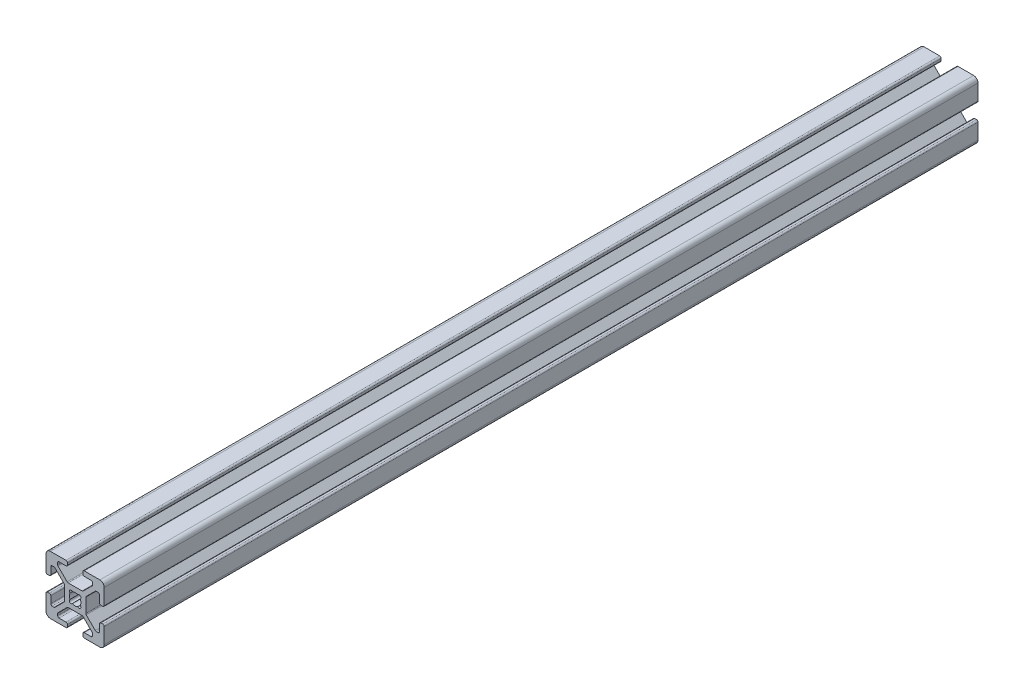
SolidWorks part; units mm, degrees
ref_plane "Front Plane" through (0, 0, 0) normal (0, 0, 1) x (1, 0, 0)
ref_plane "Top Plane" through (0, 0, 0) normal (0, 1, 0) x (1, 0, 0)
ref_plane "Right Plane" through (0, 0, 0) normal (1, 0, 0) x (0, 0, -1)
sketch "Sketch1" plane through (0, 0, 0) normal (0, 0, 1) x (1, 0, 0)
  line L0 (-2.7464, -3.807) -> (-5.848, -6.9086)
  line L1 (-8.5, -10) -> (-3.1319, -10)
  line L2 (-10, -8.5) -> (-10, -3.1319)
  line L3 (-8.5, 10) -> (-3.1319, 10)
  line L4 (10, -8.5) -> (10, -3.1319)
  line L6 (-10, 10) -> (-8.36, 8.36) construction
  line L7 (-2.3914, -3.66) -> (2.3914, -3.66)
  line L8 (-3.66, -2.3914) -> (-3.66, 2.3914)
  line L9 (-2.3914, 3.66) -> (2.3914, 3.66)
  line L10 (3.66, -2.3914) -> (3.66, 2.3914)
  line L13 (-5.4931, -8.36) -> (-3.1319, -8.36)
  line L14 (2.7464, -3.807) -> (5.848, -6.9086)
  line L15 (3.807, -2.7464) -> (6.9086, -5.848)
  line L16 (-5.995, -14.365) -> (5.995, -14.365)
  line L17 (2.63, -9.4981) -> (2.63, -8.8619)
  line L18 (8.8619, -2.63) -> (9.4981, -2.63)
  line L19 (5.995, -7.8581) -> (5.995, -7.2636)
  line L20 (-10, 3.1319) -> (-10, 8.5)
  line L22 (7.2636, -5.995) -> (7.8581, -5.995)
  line L23 (8.36, -5.4931) -> (8.36, -3.1319)
  line L24 (-3.807, -2.7464) -> (-6.9086, -5.848)
  line L25 (-9.4981, -2.63) -> (-8.8619, -2.63)
  line L26 (-7.8581, -5.995) -> (-7.2636, -5.995)
  line L27 (-5.995, -7.2636) -> (-5.995, -7.8581)
  line L28 (-2.63, -8.8619) -> (-2.63, -9.4981)
  line L30 (-5.4931, -8.36) -> (-3.1319, -8.36)
  line L31 (-3.807, 2.7464) -> (-6.9086, 5.848)
  line L32 (-2.7464, 3.807) -> (-5.848, 6.9086)
  line L33 (-2.63, 9.4981) -> (-2.63, 8.8619)
  line L34 (-5.995, 7.8581) -> (-5.995, 7.2636)
  line L35 (-7.2636, 5.995) -> (-7.8581, 5.995)
  line L36 (-8.8619, 2.63) -> (-9.4981, 2.63)
  line L37 (3.1319, 10) -> (8.5, 10)
  line L38 (-8.36, 5.4931) -> (-8.36, 3.1319)
  line L39 (2.7464, 3.807) -> (5.848, 6.9086)
  line L40 (3.807, 2.7464) -> (6.9086, 5.848)
  line L41 (9.4981, 2.63) -> (8.8619, 2.63)
  line L42 (7.8581, 5.995) -> (7.2636, 5.995)
  line L43 (5.995, 7.2636) -> (5.995, 7.8581)
  line L44 (2.63, 8.8619) -> (2.63, 9.4981)
  line L45 (8.36, -5.4931) -> (8.36, -3.1319)
  line L46 (5.4931, 8.36) -> (3.1319, 8.36)
  line L49 (-8.36, 5.4931) -> (-8.36, 3.1319)
  line L50 (5.4931, 8.36) -> (3.1319, 8.36)
  line L51 (-3.1319, 8.36) -> (-5.4931, 8.36)
  line L52 (-3.1319, 8.36) -> (-5.4931, 8.36)
  line L53 (10, 8.36) -> (8.36, 8.36) [skipped]
  line L54 (10, 3.1319) -> (10, 8.5)
  line L55 (8.36, 3.1319) -> (8.36, 5.4931)
  line L56 (8.36, 3.1319) -> (8.36, 5.4931)
  line L57 (3.1319, -8.36) -> (5.4931, -8.36)
  line L58 (3.1319, -8.36) -> (5.4931, -8.36)
  line L59 (3.1319, -10) -> (8.5, -10)
  line L60 (-8.36, -3.1319) -> (-8.36, -5.4931)
  line L61 (-8.36, -3.1319) -> (-8.36, -5.4931)
  line L62 (-8.36, 10) -> (-8.36, 8.36) [skipped]
  arc A0 (-8.5, -10) -> (-10, -8.5) centre (-8.5, -8.5) cw
  arc A1 (8.5, -10) -> (10, -8.5) centre (8.5, -8.5) ccw
  arc A2 (10, 8.5) -> (8.5, 10) centre (8.5, 8.5) ccw
  arc A3 (-8.5, 10) -> (-10, 8.5) centre (-8.5, 8.5) ccw
  arc A4 (10, -3.1319) -> (9.4981, -2.63) centre (9.4981, -3.1319) ccw
  arc A5 (8.8619, -2.63) -> (8.36, -3.1319) centre (8.8619, -3.1319) ccw
  arc A6 (7.8581, -5.995) -> (8.36, -5.4931) centre (7.8581, -5.4931) ccw
  arc A7 (7.2636, -5.995) -> (6.9086, -5.848) centre (7.2636, -5.4931) cw
  arc A8 (5.995, -7.2636) -> (5.848, -6.9086) centre (5.4931, -7.2636) ccw
  arc A9 (5.995, -7.8581) -> (5.4931, -8.36) centre (5.4931, -7.8581) cw
  arc A10 (3.1319, -10) -> (2.63, -9.4981) centre (3.1319, -9.4981) cw
  arc A11 (2.63, -8.8619) -> (3.1319, -8.36) centre (3.1319, -8.8619) cw
  arc A12 (-3.1319, -10) -> (-2.63, -9.4981) centre (-3.1319, -9.4981) ccw
  arc A13 (-2.63, -8.8619) -> (-3.1319, -8.36) centre (-3.1319, -8.8619) ccw
  arc A14 (-5.4931, -8.36) -> (-5.995, -7.8581) centre (-5.4931, -7.8581) cw
  arc A15 (-5.995, -7.2636) -> (-5.848, -6.9086) centre (-5.4931, -7.2636) cw
  arc A16 (-9.4981, -2.63) -> (-10, -3.1319) centre (-9.4981, -3.1319) ccw
  arc A17 (-8.36, -3.1319) -> (-8.8619, -2.63) centre (-8.8619, -3.1319) ccw
  arc A18 (-7.2636, -5.995) -> (-6.9086, -5.848) centre (-7.2636, -5.4931) ccw
  arc A19 (-7.8581, -5.995) -> (-8.36, -5.4931) centre (-7.8581, -5.4931) cw
  arc A20 (-3.807, -2.7464) -> (-3.66, -2.3914) centre (-4.1619, -2.3914) ccw
  arc A21 (-2.3914, -3.66) -> (-2.7464, -3.807) centre (-2.3914, -4.1619) ccw
  arc A22 (2.7464, -3.807) -> (2.3914, -3.66) centre (2.3914, -4.1619) ccw
  arc A23 (3.807, -2.7464) -> (3.66, -2.3914) centre (4.1619, -2.3914) cw
  arc A24 (9.4981, 2.63) -> (10, 3.1319) centre (9.4981, 3.1319) ccw
  arc A25 (8.8619, 2.63) -> (8.36, 3.1319) centre (8.8619, 3.1319) cw
  arc A26 (5.848, 6.9086) -> (5.995, 7.2636) centre (5.4931, 7.2636) ccw
  arc A27 (7.2636, 5.995) -> (6.9086, 5.848) centre (7.2636, 5.4931) ccw
  arc A28 (8.36, 5.4931) -> (7.8581, 5.995) centre (7.8581, 5.4931) ccw
  arc A29 (5.995, 7.8581) -> (5.4931, 8.36) centre (5.4931, 7.8581) ccw
  arc A30 (3.66, 2.3914) -> (3.807, 2.7464) centre (4.1619, 2.3914) cw
  arc A31 (-3.66, 2.3914) -> (-3.807, 2.7464) centre (-4.1619, 2.3914) ccw
  arc A32 (2.3914, 3.66) -> (2.7464, 3.807) centre (2.3914, 4.1619) ccw
  arc A33 (-2.3914, 3.66) -> (-2.7464, 3.807) centre (-2.3914, 4.1619) cw
  arc A34 (3.1319, 8.36) -> (2.63, 8.8619) centre (3.1319, 8.8619) cw
  arc A35 (2.63, 9.4981) -> (3.1319, 10) centre (3.1319, 9.4981) cw
  arc A36 (-9.4981, 2.63) -> (-10, 3.1319) centre (-9.4981, 3.1319) cw
  arc A37 (-8.8619, 2.63) -> (-8.36, 3.1319) centre (-8.8619, 3.1319) ccw
  arc A38 (-3.1319, 8.36) -> (-2.63, 8.8619) centre (-3.1319, 8.8619) ccw
  arc A39 (-2.63, 9.4981) -> (-3.1319, 10) centre (-3.1319, 9.4981) ccw
  arc A40 (-5.848, 6.9086) -> (-5.995, 7.2636) centre (-5.4931, 7.2636) cw
  arc A41 (-5.4931, 8.36) -> (-5.995, 7.8581) centre (-5.4931, 7.8581) ccw
  arc A42 (-6.9086, 5.848) -> (-7.2636, 5.995) centre (-7.2636, 5.4931) ccw
  arc A43 (-7.8581, 5.995) -> (-8.36, 5.4931) centre (-7.8581, 5.4931) ccw
  arc A44 (-1.7677, 0.9356) -> (-1.7677, -0.9356) centre (0, 0) ccw
  arc A45 (-0.9356, 1.7677) -> (-1.7677, 0.9356) centre (-1.4142, 1.4142) ccw
  arc A46 (1.7677, 0.9356) -> (0.9356, 1.7677) centre (1.4142, 1.4142) ccw
  arc A47 (0.9356, -1.7677) -> (1.7677, -0.9356) centre (1.4142, -1.4142) ccw
  arc A48 (-1.7677, -0.9356) -> (-0.9356, -1.7677) centre (-1.4142, -1.4142) ccw
  arc A49 (-0.9356, -1.7677) -> (0.9356, -1.7677) centre (0, 0) ccw
  arc A50 (1.7677, -0.9356) -> (1.7677, 0.9356) centre (0, 0) ccw
  arc A51 (0.9356, 1.7677) -> (-0.9356, 1.7677) centre (0, 0) ccw
  point P0 (0, 0)
  point P5 (0, 0)
  point P9 (-10, -10)
  point P11 (0, -10)
  point P14 (0, -3.66)
  point P23 (3.66, 0)
  point P66 (0, 0)
  point P70 (0, 0)
  dimension "D2" = 1.5
  dimension "D5" = 0.5019
  dimension "D6" = 4
  dimension "D7" = 1.19
  dimension "D1" = 20
  dimension "D3" = 11.99
  dimension "D4" = 4
  dimension "D8" = 4
extrude "Boss-Extrude1" add sketch "Sketch1" along normal blind 300 contours A43 L35 A42 L31 A31 L8 A20 L24 A18 L26 A19 L60 A17 L25 A16 L2 A0 L1 A12 L28 A13 L13 A14 L27 A15 L0 A21 L7 A22 L14 A8 L19 A9 L57 A11 L17 A10 L59 A1 L4 A4 L18 A5 L23 A6 L22 A7 L15 A23 L10 A30
